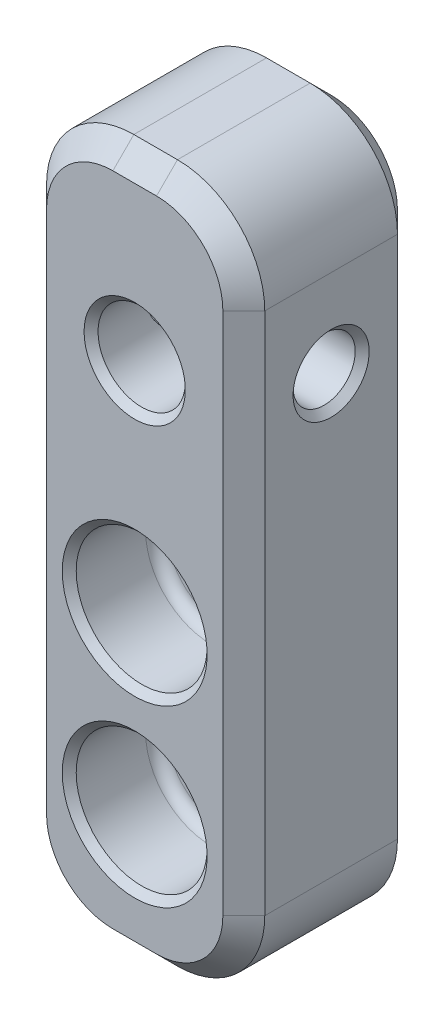
SolidWorks part; units mm, degrees
ref_plane "Front Plane" through (0, 0, 0) normal (0, 0, 1) x (1, 0, 0)
ref_plane "Top Plane" through (0, 0, 0) normal (0, 1, 0) x (1, 0, 0)
ref_plane "Right Plane" through (0, 0, 0) normal (1, 0, 0) x (0, 0, -1)
sketch "Sketch1" plane through (0, 0, 0) normal (0, 0, 1) x (1, 0, 0)
  line L1 (-3.9688, -12.7) -> (3.9688, -12.7)
  line L2 (-3.9688, -12.7) -> (-3.9688, 12.7)
  line L3 (-3.9688, 12.7) -> (3.9688, 12.7)
  line L4 (3.9688, -12.7) -> (3.9688, 12.7)
  line L5 (-3.9688, -12.7) -> (3.9688, 12.7) construction
  line L6 (-3.9688, 12.7) -> (3.9688, -12.7) construction
  point P0 (0, 0)
  dimension "D1" = 25.4
  dimension "D2" = 7.9375
extrude "Boss-Extrude1" add sketch "Sketch1" along normal mid plane 6.35 contours L3 L4 L1 L2
hole_wizard "1/8 (0.125) Diameter Hole1" positions "Sketch2" profile "Sketch3" hole size "1/8" standard "ANSI Inch" end condition through all
sketch "Sketch2" plane through (0, 0, 3.175) normal (0, 0, 1) x (1, 0, 0)
  line L0 (-3.9688, -12.7) -> (3.9688, -12.7) construction
  point P0 (0, 6.35)
  dimension "D1" = 19.05
sketch "Sketch3" plane through (0, 6.35, 3.175) normal (1, 0, 0) x (0, -1, 0)
  line L0 (0, 0) -> (0, 6.35)
  line L1 (0, 6.35) -> (1.5875, 6.35)
  line L2 (1.5875, 6.35) -> (1.5875, 0)
  line L5 (1.5875, 0) -> (0, 0)
  line L11 (0, -6.35) -> (0, 107.95) construction
  dimension "Thru Hole Dia." = 3.175
  dimension "Thru Hole Depth" = 6.35
hole_wizard "CBORE for #2 Binding Head Machine Screw1" positions "Sketch4" profile "Sketch5" counterbore size "#2" standard "ANSI Inch" end condition through all
sketch "Sketch4" plane through (0, 0, 3.175) normal (0, 0, 1) x (1, 0, 0)
  line L0 (-3.9688, -12.7) -> (3.9688, -12.7) construction
  point P0 (0, -1.5875)
  point P2 (0, -7.9375)
  dimension "D1" = 4.7625
  dimension "D2" = 6.35
sketch "Sketch5" plane through (0, -1.5875, 3.175) normal (1, 0, 0) x (0, -1, 0)
  line L0 (0, 0) -> (0, 6.35)
  line L1 (0, 6.35) -> (1.2192, 6.35)
  line L3 (1.2192, 6.35) -> (1.2192, 3.175)
  line L4 (1.2192, 3.175) -> (2.3812, 3.175)
  line L5 (2.3812, 3.175) -> (2.3812, 0)
  line L7 (2.3812, 0) -> (0, 0)
  line L11 (0, -6.35) -> (0, 107.95) construction
  dimension "Thru Hole Dia." = 2.4384
  dimension "Thru Hole Depth" = 6.35
  dimension "C'Bore Dia." = 4.7625
  dimension "C'Bore Depth" = 3.175
hole_wizard "#4-40 Tapped Hole1" positions "Sketch6" profile "Sketch7" tap size "#4-40" standard "ANSI Inch" end condition through all
sketch "Sketch6" plane through (-3.9688, 0, 0) normal (-1, 0, 0) x (0, 0, 1)
  point P0 (0, 6.35)
  dimension "D1" = 6.35
sketch "Sketch7" plane through (-3.9688, 6.35, 0) normal (0, 1, 0) x (0, 0, 1)
  line L0 (0, 0) -> (0, 7.9375)
  line L1 (0, 7.9375) -> (1.1303, 7.9375)
  line L2 (1.1303, 7.9375) -> (1.1303, 0)
  line L5 (1.1303, 0) -> (0, 0)
  line L11 (0, -6.35) -> (0, 107.95) construction
  dimension "Thru Tap Drill Dia." = 2.2606
  dimension "Thru Tap Drill Depth" = 7.9375
cosmetic thread "Hole Thread1" parameters "D2"=2.8448
fillet "Fillet1" radius 3.175 4 edges at (3.9688, 12.7, 0) (3.9688, -12.7, 0) (-3.9688, -12.7, 0) (-3.9688, 12.7, 0)
fillet "Fillet2" radius 0.3969 2 edges at (2.3812, -7.9375, 0) (2.3812, -1.5875, 0)
chamfer "Chamfer2" distance 0.762 angle 45 16 edges at (-3.0388, 11.7701, -3.175) (-3.9688, 0, -3.175) (-3.0388, -11.7701, -3.175) (0, -12.7, -3.175) (3.0388, -11.7701, -3.175) (3.9688, 0, -3.175) (3.0388, 11.7701, -3.175) (0, 12.7, -3.175) (3.0388, -11.7701, 3.175) (0, -12.7, 3.175) (-3.0388, -11.7701, 3.175) (-3.9688, 0, 3.175) (-3.0388, 11.7701, 3.175) (0, 12.7, 3.175) (3.0388, 11.7701, 3.175) (3.9688, 0, 3.175)
chamfer "Chamfer3" distance 0.254 angle 45 10 edges at (2.3812, -7.9375, 3.175) (1.2192, -7.9375, 0) (1.2192, -7.9375, -3.175) (1.2192, -1.5875, -3.175) (1.2192, -1.5875, 0) (2.3812, -1.5875, 3.175) (3.9688, 6.35, 1.1303) (-3.9688, 6.35, 1.1303) (1.5875, 6.35, -3.175) (1.5875, 6.35, 3.175)
